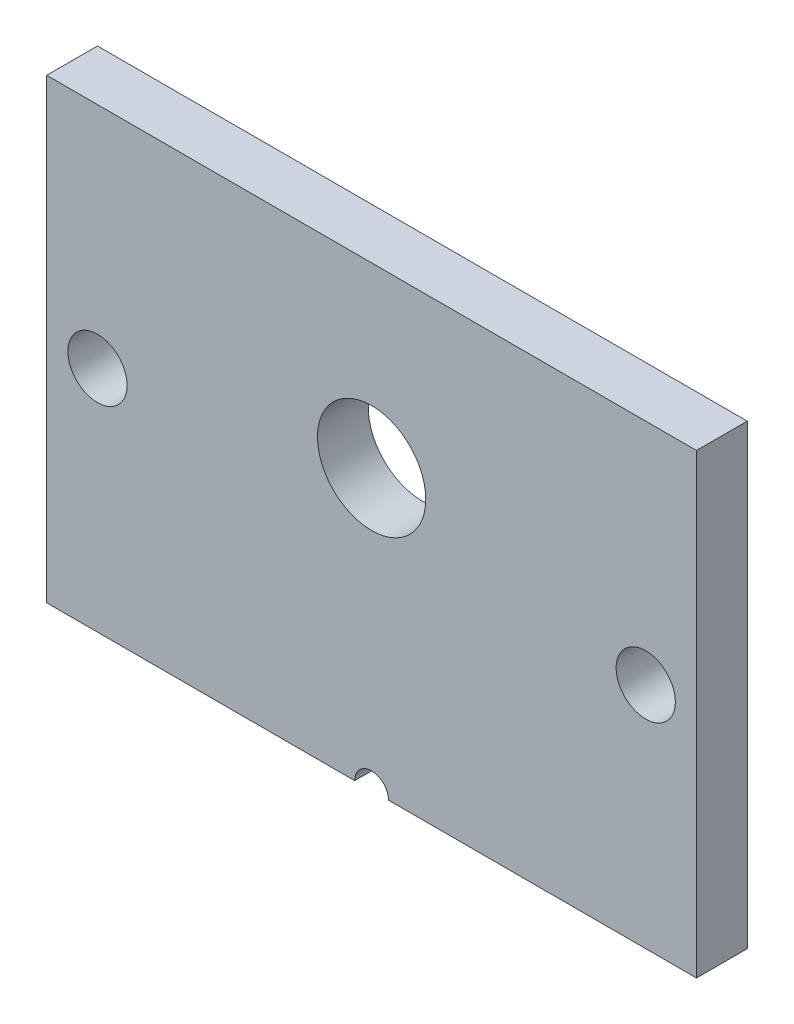
SolidWorks part; units mm, degrees
ref_plane "正面" through (0, 0, 0) normal (0, 0, 1) x (1, 0, 0)
ref_plane "平面" through (0, 0, 0) normal (0, 1, 0) x (1, 0, 0)
ref_plane "右側面" through (0, 0, 0) normal (1, 0, 0) x (0, 0, -1)
sketch "ｽｹｯﾁ1" plane through (0, 0, 0) normal (0, 0, 1) x (1, 0, 0)
  line L1 (-19.2, -13.5) -> (19.2, -13.5)
  line L2 (-19.2, -13.5) -> (-19.2, 13.5)
  line L3 (-19.2, 13.5) -> (19.2, 13.5)
  line L4 (19.2, -13.5) -> (19.2, 13.5)
  line L5 (-19.2, -13.5) -> (19.2, 13.5) construction
  line L6 (-19.2, 13.5) -> (19.2, -13.5) construction
  point P0 (0, 0)
  dimension "D1" = 38.4
  dimension "D2" = 27
extrude "ﾎﾞｽ - 押し出し1" add sketch "ｽｹｯﾁ1" along normal blind 3
sketch "ｽｹｯﾁ2" plane through (0, 0, 3) normal (0, 0, 1) x (1, 0, 0)
  line L0 (-19.2, 13.5) -> (-19.2, -13.5) construction
  line L1 (0, -13.5) -> (0, 13.5)
  line L2 (-19.2, -13.5) -> (19.2, -13.5) construction
  line L3 (19.2, 13.5) -> (-19.2, 13.5) construction
  circle A0 centre (-16.2, 0) radius 1.75
  circle A1 centre (16.2, 0) radius 1.75
  dimension "D1" = 3.5
  dimension "D2" = 3
extrude "ｶｯﾄ - 押し出し1" cut sketch "ｽｹｯﾁ2" against normal through all contours A1 | A0
sketch "ｽｹｯﾁ3" plane through (0, 0, 3) normal (0, 0, 1) x (1, 0, 0)
  line L0 (19.2, 13.5) -> (-19.2, 13.5) construction
  circle A0 centre (0, 3) radius 3.2
  dimension "D2" = 6.4
  dimension "D1" = 10.5
extrude "ｶｯﾄ - 押し出し2" cut sketch "ｽｹｯﾁ3" against normal through all
sketch "ｽｹｯﾁ4" plane through (0, 0, 3) normal (0, 0, 1) x (1, 0, 0)
  line L0 (-19.2, -13.5) -> (19.2, -13.5) construction
  circle A0 centre (0, -13.5) radius 1
  dimension "D1" = 2
extrude "ｶｯﾄ - 押し出し3" cut sketch "ｽｹｯﾁ4" against normal through all
